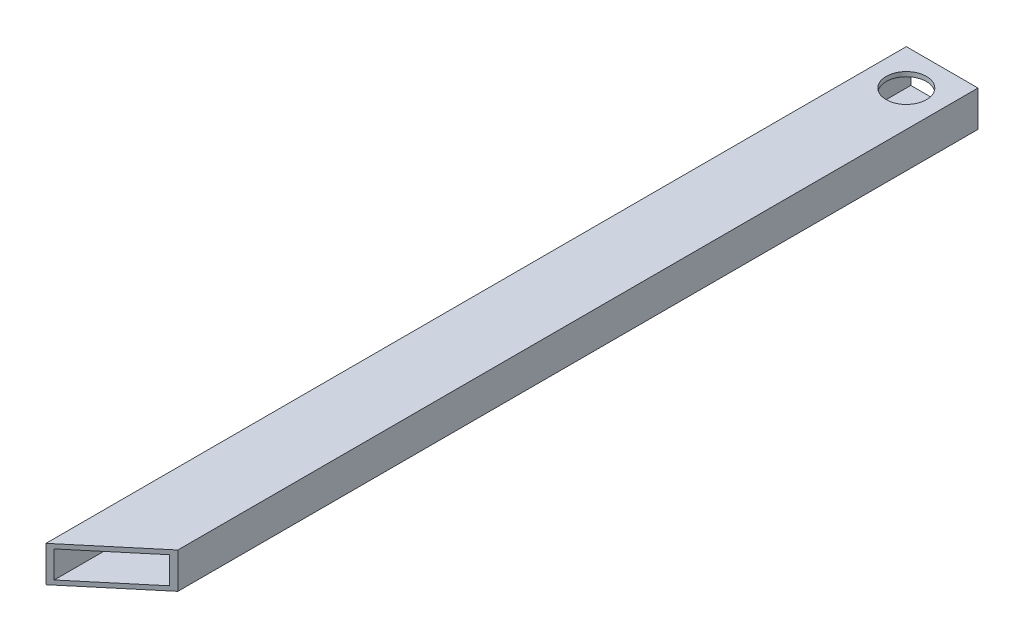
SolidWorks part; units mm, degrees
ref_plane "Front Plane" through (0, 0, 0) normal (0, 0, 1) x (1, 0, 0)
ref_plane "Top Plane" through (0, 0, 0) normal (0, 1, 0) x (1, 0, 0)
ref_plane "Right Plane" through (0, 0, 0) normal (1, 0, 0) x (0, 0, -1)
sketch "Sketch1" plane through (0, 0, 0) normal (0, 0, 1) x (1, 0, 0)
  line L1 (0, 0) -> (50.8, 0)
  line L2 (0, 0) -> (0, 25.4)
  line L3 (0, 25.4) -> (50.8, 25.4)
  line L4 (50.8, 0) -> (50.8, 25.4)
extrude "Boss-Extrude1" add sketch "Sketch1" along normal blind 609.6
sketch "Sketch2" plane through (0, 0, 0) normal (0, 0, -1) x (-1, 0, 0)
  line L1 (-3.175, 3.175) -> (-47.625, 3.175)
  line L2 (-3.175, 3.175) -> (-3.175, 22.225)
  line L3 (-3.175, 22.225) -> (-47.625, 22.225)
  line L4 (-47.625, 3.175) -> (-47.625, 22.225)
extrude "Cut-Extrude1" cut sketch "Sketch2" against normal blind 609.6
sketch "Sketch6" plane through (0, 25.4, 0) normal (0, 1, 0) x (1, 0, 0)
  line L0 (25.4, 0) -> (25.4, -25.4) construction
  line L1 (50.8, 0) -> (0, 0) construction
  circle A0 centre (25.4, -25.4) radius 14.2875
extrude "Cut-Extrude5" cut sketch "Sketch6" against normal blind 25.4
sketch "Sketch7" plane through (0, 25.4, 0) normal (0, 1, 0) x (1, 0, 0)
  line L1 (50.8, -609.6) -> (50.8, 0) construction
  line L2 (50.8, -566.9737) -> (50.8, -609.6)
  line L3 (50.8, -609.6) -> (0, -609.6)
  line L4 (50.8, -566.9737) -> (0, -609.6)
  dimension "D1" = 50
extrude "Cut-Extrude6" cut sketch "Sketch7" against normal blind 25.4
sketch "Sketch8" plane through (0, 0, 0) normal (0, -1, 0) x (1, 0, 0)
  circle A0 centre (25.4, 522.7626) radius 14.2875
extrude "Cut-Extrude7" cut sketch "Sketch8" against normal blind 3.175
